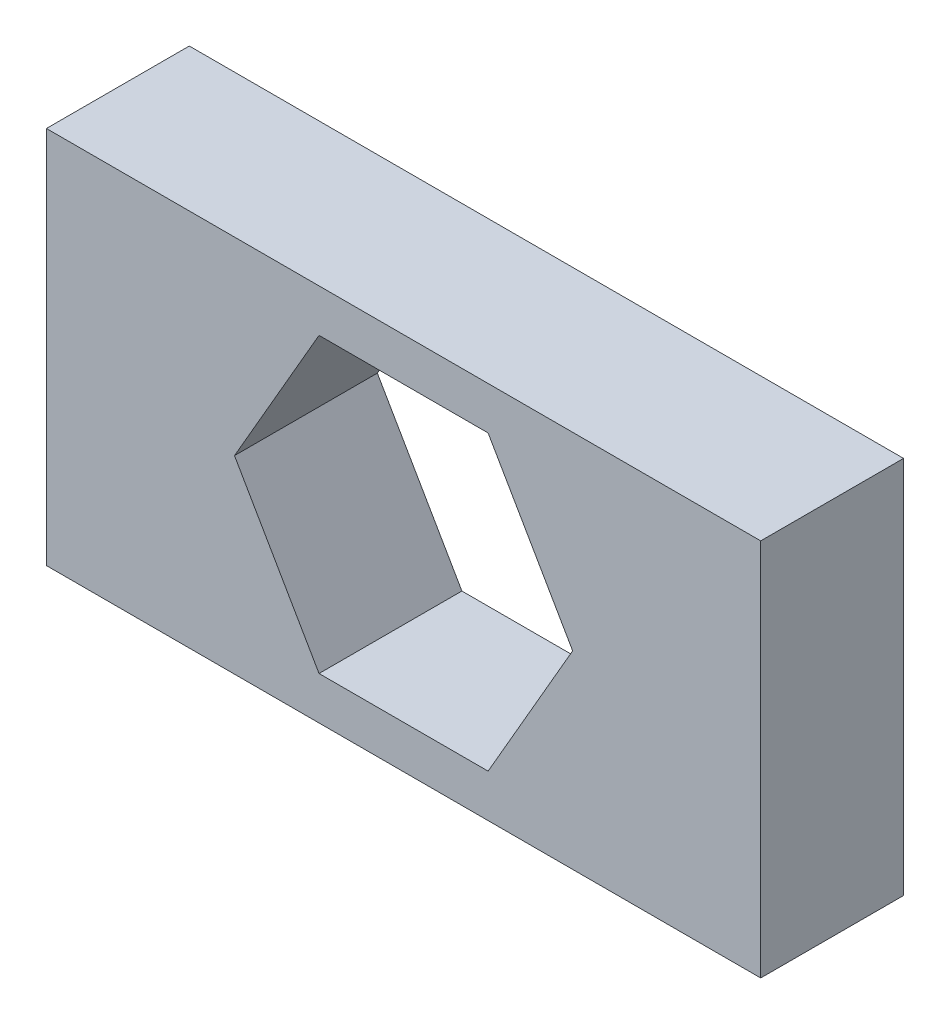
SolidWorks part; units mm, degrees
ref_plane "Plano frontal" through (0, 0, 0) normal (0, 0, 1) x (1, 0, 0)
ref_plane "Plano superior" through (0, 0, 0) normal (0, 1, 0) x (1, 0, 0)
ref_plane "Plano direito" through (0, 0, 0) normal (1, 0, 0) x (0, 0, -1)
sketch "Esboço1" plane through (0, 0, 0) normal (0, 0, 1) x (1, 0, 0)
  line L1 (-5, 2.65) -> (5, 2.65)
  line L2 (-5, 2.65) -> (-5, -2.65)
  line L3 (-5, -2.65) -> (5, -2.65)
  line L4 (5, 2.65) -> (5, -2.65)
  line L5 (-5, 2.65) -> (5, -2.65) construction
  line L6 (-5, -2.65) -> (5, 2.65) construction
  line L7 (2.3671, 0) -> (1.1836, 2.05)
  line L8 (1.1836, 2.05) -> (-1.1836, 2.05)
  line L9 (-1.1836, 2.05) -> (-2.3671, 0)
  line L10 (-2.3671, 0) -> (-1.1836, -2.05)
  line L11 (-1.1836, -2.05) -> (1.1836, -2.05)
  line L12 (1.1836, -2.05) -> (2.3671, 0)
  circle A0 centre (0, 0) radius 2.05 construction
  point P0 (0, 0)
  dimension "D1" = 4.1
  dimension "D2" = 5.3
  dimension "D3" = 0.6
  dimension "D4" = 10
extrude "Ressalto-extrusão1" add sketch "Esboço1" along normal blind 2
